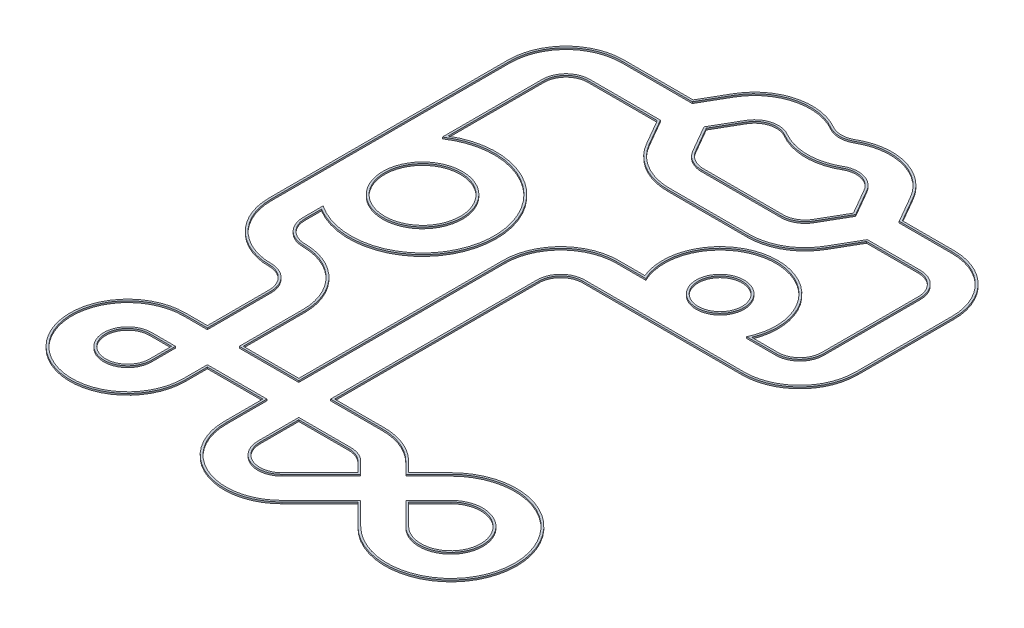
SolidWorks part; units mm, degrees
ref_plane "前视基准面" through (0, 0, 0) normal (0, 0, 1) x (1, 0, 0)
ref_plane "上视基准面" through (0, 0, 0) normal (0, 1, 0) x (1, 0, 0)
ref_plane "右视基准面" through (0, 0, 0) normal (1, 0, 0) x (0, 0, -1)
sketch "草图1" plane through (0, 0, 0) normal (0, 1, 0) x (1, 0, 0)
  line L0 (0, 0) -> (0, -2000) construction
  line L1 (500, 500) -> (1500, 500) construction
  line L2 (1500, 500) -> (1750, 933.0127) construction
  line L3 (1500, 500) -> (1750, 66.9873) construction
  line L4 (2183.0127, -183.0127) -> (3183.0127, -183.0127) construction
  line L5 (3616.0254, 933.0127) -> (3866.0254, 500) construction
  line L6 (3866.0254, 500) -> (4646.4466, 500) construction
  line L7 (3616.0254, 66.9873) -> (3866.0254, 500) construction
  line L8 (5146.4466, 0) -> (5146.4466, -1212.132) construction
  line L9 (4646.4466, -1712.132) -> (3646.4466, -1712.132) construction
  line L10 (3646.4466, -1712.132) -> (2646.4466, -1712.132) construction
  line L11 (2146.4466, -2212.132) -> (2146.4466, -5712.132) construction
  line L12 (3000, -6065.6854) -> (4060.6602, -5005.0253) construction
  line L13 (4060.6602, -5853.5534) -> (3353.5534, -5146.4466) construction
  line L14 (3000, -5000) -> (500, -5000) construction
  line L15 (1000, -5500) -> (1000, -4000) construction
  line L16 (0, -3000) -> (0, -2000) construction
  line L17 (500, 700) -> (1384.5299, 700)
  line L18 (-200, 0) -> (-200, -2000)
  line L19 (1730.9401, 500) -> (1923.2051, 833.0127)
  line L20 (3442.8203, 833.0127) -> (3635.0853, 500)
  line L21 (1384.5299, 300) -> (1576.7949, -33.0127)
  line L22 (2183.0127, -383.0127) -> (3183.0127, -383.0127)
  line L23 (3789.2305, -33.0127) -> (3981.4955, 300)
  line L24 (3981.4955, 300) -> (4646.4466, 300)
  line L25 (4946.4466, 0) -> (4946.4466, -1212.132)
  line L26 (4646.4466, -1512.132) -> (4278.9021, -1512.132)
  line L27 (500, 300) -> (1384.5299, 300)
  line L28 (200, 0) -> (200, -1251.6685)
  line L29 (1384.5299, 700) -> (1576.7949, 1033.0127)
  line L30 (3789.2305, 1033.0127) -> (3981.4955, 700)
  line L31 (1730.9401, 500) -> (1923.2051, 166.9873)
  line L32 (2183.0127, 16.9873) -> (3183.0127, 16.9873)
  line L33 (3442.8203, 166.9873) -> (3635.0853, 500)
  line L34 (3981.4955, 700) -> (4646.4466, 700)
  line L35 (5346.4466, 0) -> (5346.4466, -1212.132)
  line L36 (4646.4466, -1912.132) -> (3646.4466, -1912.132)
  line L37 (4646.4466, -1512.132) -> (3646.4466, -1512.132) construction
  line L38 (1946.4466, -2212.132) -> (1946.4466, -4800)
  line L39 (3141.4214, -6207.1068) -> (3636.3961, -5712.132)
  line L40 (3646.4466, -1912.132) -> (2646.4466, -1912.132)
  line L41 (2346.4466, -2212.132) -> (2346.4466, -4800)
  line L42 (2858.5786, -5924.2641) -> (3353.5534, -5429.2893)
  line L43 (4202.0815, -5712.132) -> (3919.2388, -5429.2893)
  line L44 (3000, -4800) -> (2346.4466, -4800)
  line L45 (3919.2388, -5994.9747) -> (3636.3961, -5712.132)
  line L46 (3000, -5200) -> (2346.4466, -5200)
  line L47 (1200, -5500) -> (1200, -5200)
  line L48 (200, -3000) -> (200, -2748.3315)
  line L49 (800, -5500) -> (800, -5200)
  line L50 (-200, -3000) -> (-200, -2000)
  line L51 (1326.7949, 600) -> (1576.7949, 1033.0127) construction
  line L52 (500, 700) -> (1500, 700) construction
  line L53 (1326.7949, 400) -> (1576.7949, -33.0127) construction
  line L54 (500, 300) -> (1500, 300) construction
  line L55 (1673.2051, 600) -> (1923.2051, 166.9873) construction
  line L56 (1673.2051, 400) -> (1923.2051, 833.0127) construction
  line L57 (3442.8203, 833.0127) -> (3692.8203, 400) construction
  line L58 (3442.8203, 166.9873) -> (3692.8203, 600) construction
  line L59 (3866.0254, 700) -> (4646.4466, 700) construction
  line L60 (3789.2305, 1033.0127) -> (4039.2305, 600) construction
  line L61 (3866.0254, 300) -> (4646.4466, 300) construction
  line L62 (3789.2305, -33.0127) -> (4039.2305, 400) construction
  line L63 (3013.9911, -1512.132) -> (2646.4466, -1512.132)
  line L64 (3646.4466, -1512.132) -> (2646.4466, -1512.132) construction
  line L65 (2346.4466, -5200) -> (2346.4466, -5712.132)
  line L66 (2346.4466, -2212.132) -> (2346.4466, -5712.132) construction
  line L67 (1946.4466, -4800) -> (1200, -4800)
  line L68 (3000, -4800) -> (500, -4800) construction
  line L69 (1946.4466, -5200) -> (1946.4466, -5712.132)
  line L70 (1946.4466, -2212.132) -> (1946.4466, -5712.132) construction
  line L71 (1946.4466, -5200) -> (1200, -5200)
  line L72 (3000, -5200) -> (500, -5200) construction
  line L73 (3636.3961, -5146.4466) -> (3919.2388, -4863.6039)
  line L74 (2858.5786, -5924.2641) -> (3919.2388, -4863.6039) construction
  line L75 (3636.3961, -5146.4466) -> (3494.9747, -5005.0253)
  line L76 (4202.0815, -5712.132) -> (3494.9747, -5005.0253) construction
  line L77 (3919.2388, -5429.2893) -> (4202.0815, -5146.4466)
  line L78 (3141.4214, -6207.1068) -> (4202.0815, -5146.4466) construction
  line L79 (3353.5534, -5429.2893) -> (3212.132, -5287.868)
  line L80 (3919.2388, -5994.9747) -> (3212.132, -5287.868) construction
  line L81 (1200, -4800) -> (1200, -4000)
  line L82 (1200, -5500) -> (1200, -4000) construction
  line L83 (800, -5200) -> (500, -5200)
  line L84 (800, -4800) -> (800, -4000)
  line L85 (800, -5500) -> (800, -4000) construction
  line L86 (800, -4800) -> (500, -4800)
  line L87 (200, 0) -> (200, -2000) construction
  line L88 (200, -3000) -> (200, -2000) construction
  line L89 (4646.4466, -1937.132) -> (3646.4466, -1937.132)
  line L90 (5371.4466, 0) -> (5371.4466, -1212.132)
  line L91 (3995.9292, 725) -> (4646.4466, 725)
  line L92 (3810.8811, 1045.5127) -> (3995.9292, 725)
  line L93 (1370.0962, 725) -> (1555.1443, 1045.5127)
  line L94 (500, 725) -> (1370.0962, 725)
  line L95 (-225, 0) -> (-225, -2000)
  line L96 (3646.4466, -1937.132) -> (2646.4466, -1937.132)
  line L97 (2371.4466, -2212.132) -> (2371.4466, -4775)
  line L98 (3000, -4775) -> (2371.4466, -4775)
  line L99 (3636.3961, -5111.0913) -> (3512.6524, -4987.3476)
  line L100 (3636.3961, -5111.0913) -> (3901.5611, -4845.9262)
  line L101 (3901.5611, -6012.6524) -> (3636.3961, -5747.4874)
  line L102 (3159.099, -6224.7845) -> (3636.3961, -5747.4874)
  line L103 (1921.4466, -5225) -> (1921.4466, -5712.132)
  line L104 (1921.4466, -5225) -> (1225, -5225)
  line L105 (1225, -5500) -> (1225, -5225)
  line L106 (775, -4775) -> (500, -4775)
  line L107 (775, -4775) -> (775, -4000)
  line L108 (-225, -3000) -> (-225, -2000)
  line L109 (4646.4466, -1487.132) -> (4317.267, -1487.132)
  line L110 (4921.4466, 0) -> (4921.4466, -1212.132)
  line L111 (3995.9292, 275) -> (4646.4466, 275)
  line L112 (3810.8811, -45.5127) -> (3995.9292, 275)
  line L113 (2183.0127, -408.0127) -> (3183.0127, -408.0127)
  line L114 (1370.0962, 275) -> (1555.1443, -45.5127)
  line L115 (500, 275) -> (1370.0962, 275)
  line L116 (225, 0) -> (225, -1206.2746)
  line L117 (225, -3000) -> (225, -2793.7254)
  line L118 (1225, -4775) -> (1225, -4000)
  line L119 (1921.4466, -4775) -> (1225, -4775)
  line L120 (1921.4466, -2212.132) -> (1921.4466, -4775)
  line L121 (2975.6262, -1487.132) -> (2646.4466, -1487.132)
  line L122 (3421.1697, 820.5127) -> (3606.2178, 500)
  line L123 (3421.1697, 179.4873) -> (3606.2178, 500)
  line L124 (2183.0127, 41.9873) -> (3183.0127, 41.9873)
  line L125 (1759.8076, 500) -> (1944.8557, 179.4873)
  line L126 (1759.8076, 500) -> (1944.8557, 820.5127)
  line L127 (4219.7592, -5694.4544) -> (3954.5942, -5429.2893)
  line L128 (3954.5942, -5429.2893) -> (4219.7592, -5164.1243)
  line L129 (2840.901, -5906.5864) -> (3318.1981, -5429.2893)
  line L130 (3318.1981, -5429.2893) -> (3194.4544, -5305.5456)
  line L131 (3000, -5225) -> (2371.4466, -5225)
  line L132 (2371.4466, -5225) -> (2371.4466, -5712.132)
  line L133 (775, -5500) -> (775, -5225)
  line L134 (775, -5225) -> (500, -5225)
  arc A0 (0, 0) -> (500, 500) centre (500, 0) cw construction
  arc A1 (1750, 933.0127) -> (2433.0127, 1116.0254) centre (2183.0127, 683.0127) cw construction
  arc A2 (2433.0127, 1116.0254) -> (2933.0127, 1116.0254) centre (2683.0127, 1549.0381) ccw construction
  arc A3 (2933.0127, 1116.0254) -> (3616.0254, 933.0127) centre (3183.0127, 683.0127) cw construction
  arc A4 (1750, 66.9873) -> (2183.0127, -183.0127) centre (2183.0127, 316.9873) ccw construction
  arc A5 (3183.0127, -183.0127) -> (3616.0254, 66.9873) centre (3183.0127, 316.9873) ccw construction
  arc A6 (4646.4466, 500) -> (5146.4466, 0) centre (4646.4466, 0) cw construction
  arc A7 (5146.4466, -1212.132) -> (4646.4466, -1712.132) centre (4646.4466, -1212.132) cw construction
  arc A8 (3646.4466, -1712.132) -> (3646.4466, -712.132) centre (3646.4466, -1212.132) cw construction
  arc A9 (3646.4466, -712.132) -> (3646.4466, -1712.132) centre (3646.4466, -1212.132) cw construction
  arc A10 (2646.4466, -1712.132) -> (2146.4466, -2212.132) centre (2646.4466, -2212.132) ccw construction
  arc A11 (2146.4466, -5712.132) -> (3000, -6065.6854) centre (2646.4466, -5712.132) ccw construction
  arc A12 (4060.6602, -5005.0253) -> (4060.6602, -5853.5534) centre (4484.9242, -5429.2893) cw construction
  arc A13 (3353.5534, -5146.4466) -> (3000, -5000) centre (3000, -5500) ccw construction
  arc A14 (500, -5000) -> (1000, -5500) centre (500, -5500) ccw construction
  arc A15 (1000, -4000) -> (500, -3500) centre (500, -4000) ccw construction
  arc A16 (500, -3500) -> (0, -3000) centre (500, -3000) cw construction
  arc A17 (0, -2000) -> (1400, -2000) centre (700, -2000) cw construction
  arc A18 (1400, -2000) -> (0, -2000) centre (700, -2000) cw construction
  arc A19 (-200, 0) -> (500, 700) centre (500, 0) cw
  arc A20 (1600, -2000) -> (200, -2748.3315) centre (700, -2000) cw
  arc A21 (1923.2051, 833.0127) -> (2333.0127, 942.8203) centre (2183.0127, 683.0127) cw
  arc A22 (2333.0127, 942.8203) -> (3033.0127, 942.8203) centre (2683.0127, 1549.0381) ccw
  arc A23 (3033.0127, 942.8203) -> (3442.8203, 833.0127) centre (3183.0127, 683.0127) cw
  arc A24 (1576.7949, -33.0127) -> (2183.0127, -383.0127) centre (2183.0127, 316.9873) ccw
  arc A25 (3183.0127, -383.0127) -> (3789.2305, -33.0127) centre (3183.0127, 316.9873) ccw
  arc A26 (4646.4466, 300) -> (4946.4466, 0) centre (4646.4466, 0) cw
  arc A27 (4946.4466, -1212.132) -> (4646.4466, -1512.132) centre (4646.4466, -1212.132) cw
  arc A28 (3646.4466, -1512.132) -> (3646.4466, -912.132) centre (3646.4466, -1212.132) cw
  arc A29 (200, 0) -> (500, 300) centre (500, 0) cw
  arc A30 (1200, -2000) -> (200, -2000) centre (700, -2000) cw
  arc A31 (1576.7949, 1033.0127) -> (2533.0127, 1289.2305) centre (2183.0127, 683.0127) cw
  arc A32 (2533.0127, 1289.2305) -> (2833.0127, 1289.2305) centre (2683.0127, 1549.0381) ccw
  arc A33 (2833.0127, 1289.2305) -> (3789.2305, 1033.0127) centre (3183.0127, 683.0127) cw
  arc A34 (1923.2051, 166.9873) -> (2183.0127, 16.9873) centre (2183.0127, 316.9873) ccw
  arc A35 (3183.0127, 16.9873) -> (3442.8203, 166.9873) centre (3183.0127, 316.9873) ccw
  arc A36 (4646.4466, 700) -> (5346.4466, 0) centre (4646.4466, 0) cw
  arc A37 (5346.4466, -1212.132) -> (4646.4466, -1912.132) centre (4646.4466, -1212.132) cw
  arc A38 (3013.9911, -1512.132) -> (3646.4466, -512.132) centre (3646.4466, -1212.132) cw
  arc A39 (3646.4466, -912.132) -> (3646.4466, -1512.132) centre (3646.4466, -1212.132) cw
  arc A40 (2646.4466, -1512.132) -> (1946.4466, -2212.132) centre (2646.4466, -2212.132) ccw
  arc A41 (1946.4466, -5712.132) -> (3141.4214, -6207.1068) centre (2646.4466, -5712.132) ccw
  arc A42 (4202.0815, -5146.4466) -> (4202.0815, -5712.132) centre (4484.9242, -5429.2893) cw
  arc A43 (3646.4466, -512.132) -> (4278.9021, -1512.132) centre (3646.4466, -1212.132) cw
  arc A44 (2646.4466, -1912.132) -> (2346.4466, -2212.132) centre (2646.4466, -2212.132) ccw
  arc A45 (2346.4466, -5712.132) -> (2858.5786, -5924.2641) centre (2646.4466, -5712.132) ccw
  arc A46 (3919.2388, -4863.6039) -> (3919.2388, -5994.9747) centre (4484.9242, -5429.2893) cw
  arc A47 (3494.9747, -5005.0253) -> (3000, -4800) centre (3000, -5500) ccw
  arc A48 (500, -4800) -> (1200, -5500) centre (500, -5500) ccw
  arc A49 (3212.132, -5287.868) -> (3000, -5200) centre (3000, -5500) ccw
  arc A50 (500, -5200) -> (800, -5500) centre (500, -5500) ccw
  arc A51 (1200, -4000) -> (500, -3300) centre (500, -4000) ccw
  arc A52 (500, -3300) -> (200, -3000) centre (500, -3000) cw
  arc A53 (200, -2000) -> (1200, -2000) centre (700, -2000) cw
  arc A54 (800, -4000) -> (500, -3700) centre (500, -4000) ccw
  arc A55 (500, -3700) -> (-200, -3000) centre (500, -3000) cw
  arc A56 (5371.4466, -1212.132) -> (4646.4466, -1937.132) centre (4646.4466, -1212.132) cw
  arc A57 (3646.4466, -512.132) -> (3646.4466, -1912.132) centre (3646.4466, -1212.132) cw construction
  arc A58 (3646.4466, -1912.132) -> (3646.4466, -512.132) centre (3646.4466, -1212.132) cw construction
  arc A59 (4646.4466, 725) -> (5371.4466, 0) centre (4646.4466, 0) cw
  arc A60 (1600, -2000) -> (-200, -2000) centre (700, -2000) cw construction
  arc A61 (200, -1251.6685) -> (1600, -2000) centre (700, -2000) cw
  arc A62 (-200, -2000) -> (1600, -2000) centre (700, -2000) cw construction
  arc A63 (2820.5127, 1310.8811) -> (3810.8811, 1045.5127) centre (3183.0127, 683.0127) cw
  arc A64 (2545.5127, 1310.8811) -> (2820.5127, 1310.8811) centre (2683.0127, 1549.0381) ccw
  arc A65 (1555.1443, 1045.5127) -> (2545.5127, 1310.8811) centre (2183.0127, 683.0127) cw
  arc A66 (-225, 0) -> (500, 725) centre (500, 0) cw
  arc A67 (2646.4466, -1937.132) -> (2371.4466, -2212.132) centre (2646.4466, -2212.132) ccw
  arc A68 (3512.6524, -4987.3476) -> (3000, -4775) centre (3000, -5500) ccw
  arc A69 (3901.5611, -4845.9262) -> (3901.5611, -6012.6524) centre (4484.9242, -5429.2893) cw
  arc A70 (1921.4466, -5712.132) -> (3159.099, -6224.7845) centre (2646.4466, -5712.132) ccw
  arc A71 (500, -4775) -> (1225, -5500) centre (500, -5500) ccw
  arc A72 (775, -4000) -> (500, -3725) centre (500, -4000) ccw
  arc A73 (500, -3725) -> (-225, -3000) centre (500, -3000) cw
  arc A74 (3646.4466, -487.132) -> (4317.267, -1487.132) centre (3646.4466, -1212.132) cw
  arc A75 (4921.4466, -1212.132) -> (4646.4466, -1487.132) centre (4646.4466, -1212.132) cw
  arc A76 (4646.4466, 275) -> (4921.4466, 0) centre (4646.4466, 0) cw
  arc A77 (3183.0127, -408.0127) -> (3810.8811, -45.5127) centre (3183.0127, 316.9873) ccw
  arc A78 (1555.1443, -45.5127) -> (2183.0127, -408.0127) centre (2183.0127, 316.9873) ccw
  arc A79 (225, 0) -> (500, 275) centre (500, 0) cw
  arc A80 (225, -1206.2746) -> (1625, -2000) centre (700, -2000) cw
  arc A81 (1625, -2000) -> (225, -2793.7254) centre (700, -2000) cw
  arc A82 (500, -3275) -> (225, -3000) centre (500, -3000) cw
  arc A83 (1225, -4000) -> (500, -3275) centre (500, -4000) ccw
  arc A84 (2646.4466, -1487.132) -> (1921.4466, -2212.132) centre (2646.4466, -2212.132) ccw
  arc A85 (2975.6262, -1487.132) -> (3646.4466, -487.132) centre (3646.4466, -1212.132) cw
  arc A86 (3183.0127, 41.9873) -> (3421.1697, 179.4873) centre (3183.0127, 316.9873) ccw
  arc A87 (1944.8557, 179.4873) -> (2183.0127, 41.9873) centre (2183.0127, 316.9873) ccw
  arc A88 (1944.8557, 820.5127) -> (2320.5127, 921.1697) centre (2183.0127, 683.0127) cw
  arc A89 (2320.5127, 921.1697) -> (3045.5127, 921.1697) centre (2683.0127, 1549.0381) ccw
  arc A90 (3045.5127, 921.1697) -> (3421.1697, 820.5127) centre (3183.0127, 683.0127) cw
  arc A91 (3646.4466, -1487.132) -> (3646.4466, -937.132) centre (3646.4466, -1212.132) cw
  arc A92 (3646.4466, -937.132) -> (3646.4466, -1487.132) centre (3646.4466, -1212.132) cw
  arc A93 (225, -2000) -> (1175, -2000) centre (700, -2000) cw
  arc A94 (1175, -2000) -> (225, -2000) centre (700, -2000) cw
  arc A95 (4219.7592, -5164.1243) -> (4219.7592, -5694.4544) centre (4484.9242, -5429.2893) cw
  arc A96 (3194.4544, -5305.5456) -> (3000, -5225) centre (3000, -5500) ccw
  arc A97 (2371.4466, -5712.132) -> (2840.901, -5906.5864) centre (2646.4466, -5712.132) ccw
  arc A98 (500, -5225) -> (775, -5500) centre (500, -5500) ccw
  dimension "D2" = 500
  dimension "D4" = 500
  dimension "D5" = 500
  dimension "D6" = 500
  dimension "D8" = 90
  dimension "D10" = 500
  dimension "D11" = 500
  dimension "D15" = 500
  dimension "D16" = 500
  dimension "D17" = 500
  dimension "D18" = 1000
  dimension "D20" = 500
  dimension "D21" = 500
  dimension "D22" = 600
  dimension "D25" = 500
  dimension "D26" = 500
  dimension "D27" = 500
  dimension "D29" = 700
  dimension "D30" = 2000
  dimension "D34" = 500
  dimension "D38" = 1000
  dimension "D1" = 120
  dimension "D3" = 120
  dimension "D7" = 60
  dimension "D9" = 90
  dimension "D12" = 60
  dimension "D13" = 60
  dimension "D14" = 500
  dimension "D19" = 1000
  dimension "D23" = 225
  dimension "D24" = 90
  dimension "D28" = 90
  dimension "D31" = 1000
  dimension "D32" = 1500
  dimension "D33" = 2500
  dimension "D35" = 1000
  dimension "D36" = 1500
  dimension "D37" = 3500
  dimension "D39" = 200
  dimension "D40" = 200
  dimension "D41" = 200
  dimension "D42" = 200
  dimension "D43" = 200
  dimension "D44" = 200
  dimension "D45" = 200
  dimension "D46" = 200
  dimension "D47" = 25
  dimension "D48" = 25
  dimension "D49" = 25
  dimension "D50" = 25
  dimension "D51" = 25
  dimension "D52" = 25
  dimension "D53" = 25
  dimension "D54" = 25
  dimension "D55" = 25
  dimension "D56" = 25
  dimension "D57" = 25
extrude "凸台-拉伸2" add sketch "草图1" along normal blind 20 contours A73 A72 L107 L106 A71 L105 L104 L103 A70 L102 L101 A69 L100 L99 A68 L98 L97 A67 L96 L89 A56 L90 A59 L91 L92 A63 A64 A65 L93 L94 A66 L95 L108 A54 A55 L50 L18 A19 L17 L29 A31 A32 A33 L30 L34 A36 L35 A37 L36 L40 | L28 A61 A20 L48 A52 A51 L81 L67 L38 A40 L63 A38 A43 L26 A27 L25 A26 L24 L23 A25 L22 A24 L21 L27 A29 A85 L121 A84 L120 L119 L118 A83 A82 L117 A81 A80 L116 A79 L115 L114 A78 L113 A77 L112 L111 A76 L110 A75 L109 A74 | A53 A30 A93 A94 | A39 A28 A91 A92 | L32 A35 L33 L20 A23 A22 A21 L19 L31 A34 A89 A90 L122 L123 A86 L124 A87 L125 L126 A88 | L79 A49 L46 L65 A45 L42 A97 L132 L131 A96 L130 L129 | A42 L77 L43 L128 A95 L127 | L83 A50 L49 A98 L134 L133
